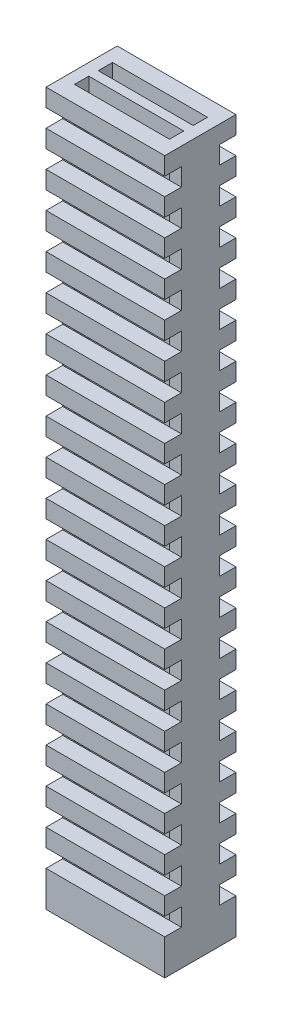
SolidWorks part; units mm, degrees
ref_plane "Front Plane" through (0, 0, 0) normal (0, 0, 1) x (1, 0, 0)
ref_plane "Top Plane" through (0, 0, 0) normal (0, 1, 0) x (1, 0, 0)
ref_plane "Right Plane" through (0, 0, 0) normal (1, 0, 0) x (0, 0, -1)
sketch "Sketch1" plane through (0, 0, 0) normal (0, 1, 0) x (1, 0, 0)
  line L1 (-2.5, -1.5) -> (2.5, -1.5)
  line L2 (-2.5, -1.5) -> (-2.5, 1.5)
  line L3 (-2.5, 1.5) -> (2.5, 1.5)
  line L4 (2.5, -1.5) -> (2.5, 1.5)
  line L5 (-2.5, -1.5) -> (2.5, 1.5) construction
  line L6 (-2.5, 1.5) -> (2.5, -1.5) construction
  point P0 (0, 0)
  dimension "D1" = 5
  dimension "D2" = 3
extrude "Boss-Extrude1" add sketch "Sketch1" along normal mid plane 30
sketch "Sketch2" plane through (0, 15, 0) normal (0, 1, 0) x (1, 0, 0)
  line L0 (-2.5, 1.5) -> (-2.5, -1.5) construction
  line L1 (-2, 0.2) -> (2, 0.2)
  line L2 (-2, 0.2) -> (-2, 0.8)
  line L3 (-2, 0.8) -> (2, 0.8)
  line L4 (2, 0.2) -> (2, 0.8)
  line L5 (-2, 0.2) -> (2, 0.8) construction
  line L6 (-2, 0.8) -> (2, 0.2) construction
  point P0 (0, 0.5)
  dimension "D1" = 0.6
  dimension "D2" = 0.5
  dimension "D3" = 0
  dimension "D4" = 0.5
extrude "Cut-Extrude1" cut sketch "Sketch2" against normal through all and the other way through all
mirror "Mirror1" about plane through (0, 0, 0) normal (0, 0, 1) of "Cut-Extrude1"
sketch "Sketch3" plane through (0, 0, 1.5) normal (0, 0, 1) x (1, 0, 0)
  line L0 (0, -1.65) -> (0, 1.65) construction
  line L1 (-2.5, 13.5) -> (2.5, 13.5)
  line L2 (-2.5, 13.5) -> (-2.5, 14.25)
  line L3 (-2.5, 14.25) -> (2.5, 14.25)
  line L4 (2.5, 13.5) -> (2.5, 14.25)
  line L5 (-2.5, 13.5) -> (2.5, 14.25) construction
  line L6 (-2.5, 14.25) -> (2.5, 13.5) construction
  line L7 (-2.5, 15) -> (2.5, 15) construction
  line L8 (2.5, 15) -> (2.5, -15) construction
  point P0 (0, 13.875)
  dimension "D1" = 0.75
  dimension "D2" = 0.75
  dimension "D3" = 0
extrude "Cut-Extrude2" cut sketch "Sketch3" against normal blind 0.7
pattern_linear "LPattern1" count 19 spacing 1.5 along (0, -1, 0) of "Cut-Extrude2"
mirror "Mirror2" about plane through (0, 0, 0) normal (0, 0, 1) of "LPattern1", "Cut-Extrude2"
